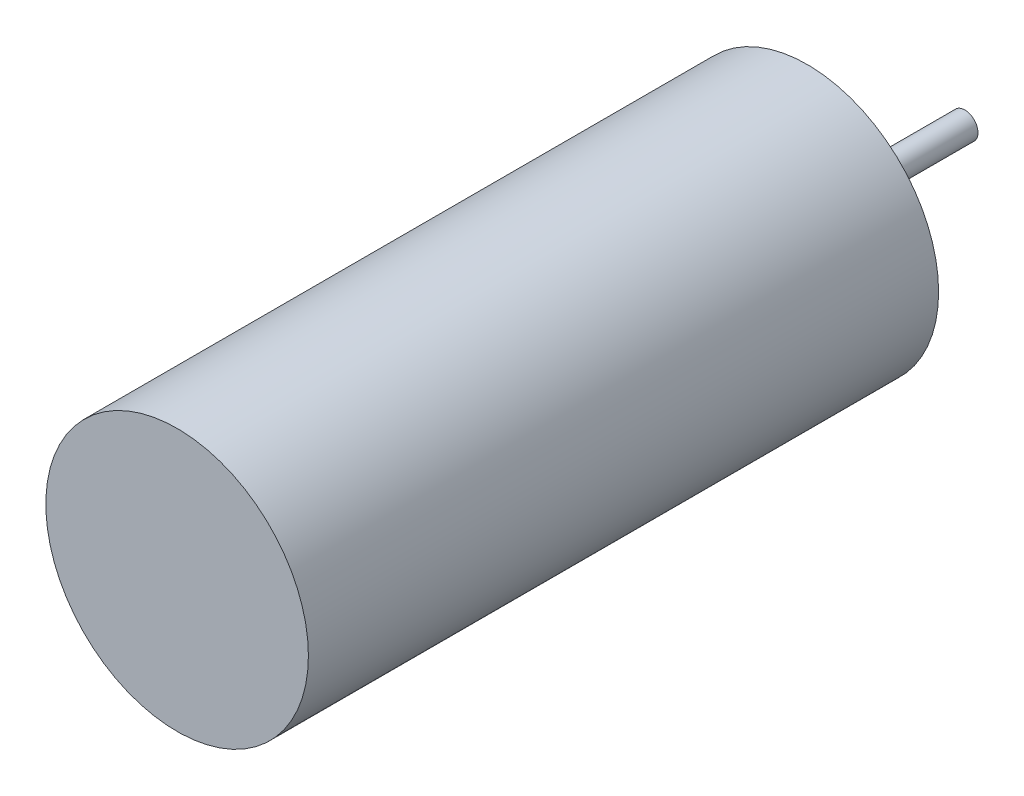
SolidWorks part; units mm, degrees
material "合金钢"
ref_plane "Front" through (0, 0, 0) normal (0, 0, 1) x (1, 0, 0)
ref_plane "Top" through (0, 0, 0) normal (0, 1, 0) x (1, 0, 0)
ref_plane "Right" through (0, 0, 0) normal (1, 0, 0) x (0, 0, -1)
sketch "草图1" plane through (0, 0, 0) normal (0, 0, 1) x (1, 0, 0)
  circle A0 centre (0, 0) radius 2.5
  dimension "D1" = 5
extrude "凸台-拉伸1" add sketch "草图1" along normal blind 12
sketch "草图2" plane through (0, 0, 0) normal (0, 0, -1) x (-1, 0, 0)
  circle A0 centre (0, 0) radius 0.25
  dimension "D1" = 0.5
extrude "凸台-拉伸2" add sketch "草图2" along normal blind 3
